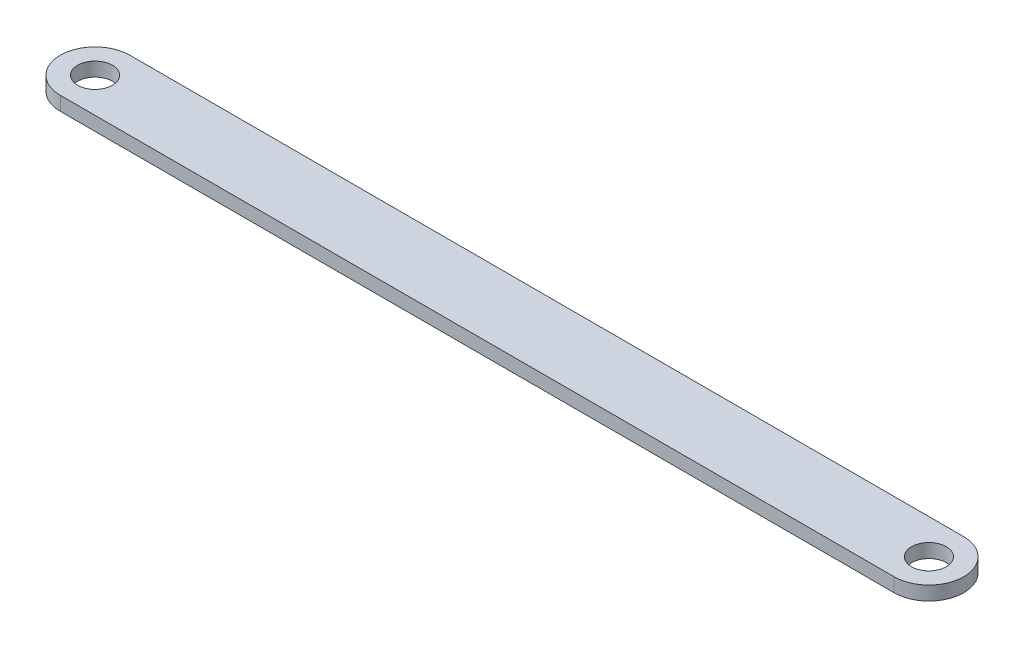
SolidWorks part; units mm, degrees
material "AISI 1020"
ref_plane "Front Plane" through (0, 0, 0) normal (0, 0, 1) x (1, 0, 0)
ref_plane "Top Plane" through (0, 0, 0) normal (0, 1, 0) x (1, 0, 0)
ref_plane "Right Plane" through (0, 0, 0) normal (1, 0, 0) x (0, 0, -1)
sketch "Sketch1" plane through (0, 0, 0) normal (0, 1, 0) x (1, 0, 0)
  line L0 (0, 0) -> (0, 20.2305) construction
  line L1 (-76.2, -6.35) -> (76.2, -6.35)
  line L3 (-76.2, 6.35) -> (76.2, 6.35)
  circle A0 centre (-76.2, 0) radius 3.175
  arc A1 (-76.2, 6.35) -> (-76.2, -6.35) centre (-76.2, 0) ccw
  circle A2 centre (76.2, 0) radius 3.175
  arc A3 (76.2, 6.35) -> (76.2, -6.35) centre (76.2, 0) cw
  point P0 (0, 0)
  dimension "D3" = 6.35
  dimension "D4" = 12.7
extrude "Boss-Extrude1" add sketch "Sketch1" along normal blind 2.54
